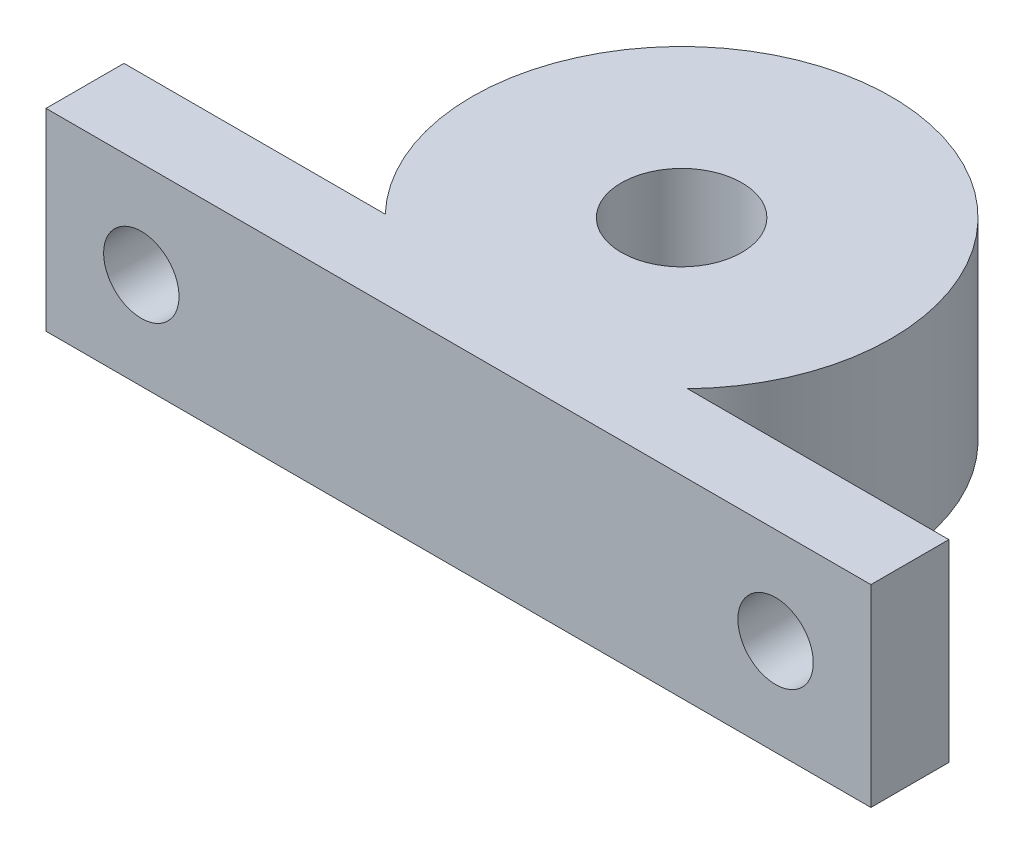
SolidWorks part; units mm, degrees
ref_plane "Front Plane" through (0, 0, 0) normal (0, 0, 1) x (1, 0, 0)
ref_plane "Top Plane" through (0, 0, 0) normal (0, 1, 0) x (1, 0, 0)
ref_plane "Right Plane" through (0, 0, 0) normal (1, 0, 0) x (0, 0, -1)
sketch "Sketch1" plane through (0, 0, 0) normal (0, 1, 0) x (1, 0, 0)
  line L0 (27.35, 0) -> (27.35, 14.8) construction
  line L1 (0, 0) -> (54.7, 0)
  line L2 (0, 0) -> (0, 5.17)
  line L3 (0, 5.17) -> (17.3264, 5.17)
  line L4 (54.7, 0) -> (54.7, 5.17)
  line L5 (37.3736, 5.17) -> (54.7, 5.17)
  circle A0 centre (27.35, 14.8) radius 4
  arc A1 (37.3736, 5.17) -> (17.3264, 5.17) centre (27.35, 14.8) ccw
  point P4 (27.35, 2.585)
  dimension "D4" = 8
  dimension "D5" = 27.8
  dimension "D1" = 54.7
  dimension "D2" = 5.17
  dimension "D3" = 14.8
extrude "Boss-Extrude1" add sketch "Sketch1" along normal blind 12.8
sketch "Sketch2" plane through (0, 0, -5.17) normal (0, 0, -1) x (-1, 0, 0)
  line L0 (-54.7, 6.4) -> (0, 6.4) construction
  line L1 (-54.7, 12.8) -> (-54.7, 0) construction
  line L2 (0, 12.8) -> (0, 0) construction
  circle A0 centre (-48.38, 6.4) radius 2.5
  circle A1 centre (-6.32, 6.4) radius 2.5
  dimension "D3" = 5
  dimension "D1" = 6.32
  dimension "D2" = 6.32
extrude "Cut-Extrude1" cut sketch "Sketch2" against normal through all
